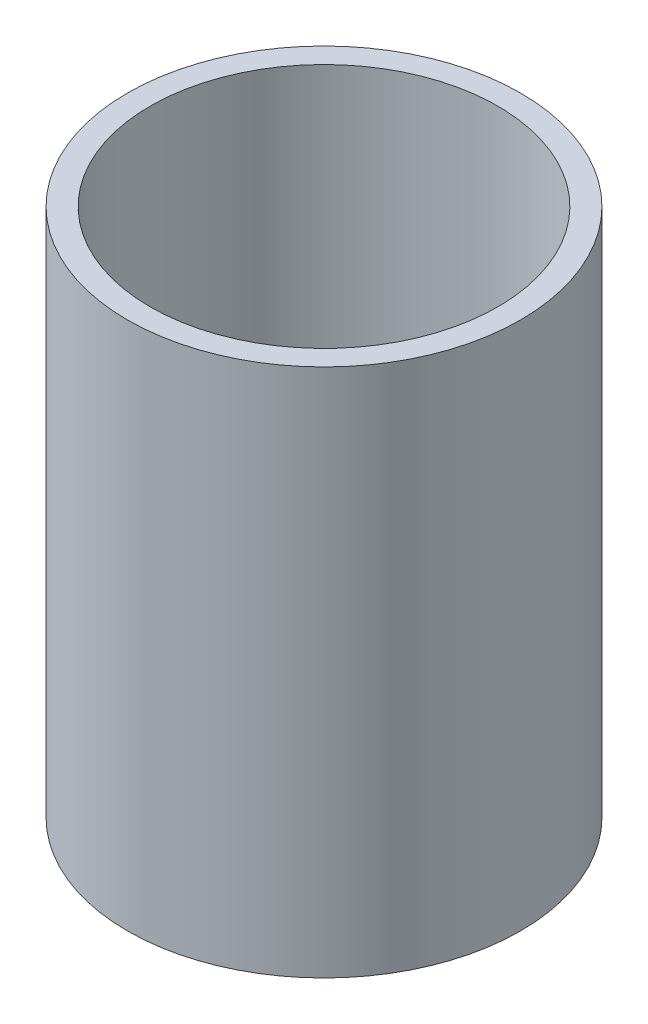
SolidWorks part; units mm, degrees
ref_plane "Front Plane" through (0, 0, 0) normal (0, 0, 1) x (1, 0, 0)
ref_plane "Top Plane" through (0, 0, 0) normal (0, 1, 0) x (1, 0, 0)
ref_plane "Right Plane" through (0, 0, 0) normal (1, 0, 0) x (0, 0, -1)
sketch "Sketch1" plane through (0, 0, 0) normal (0, 1, 0) x (1, 0, 0)
  circle A0 centre (0, 0) radius 23
  circle A1 centre (0, 0) radius 26
  dimension "D1" = 46
  dimension "D2" = 52
extrude "Boss-Extrude1" add sketch "Sketch1" along normal mid plane 70
